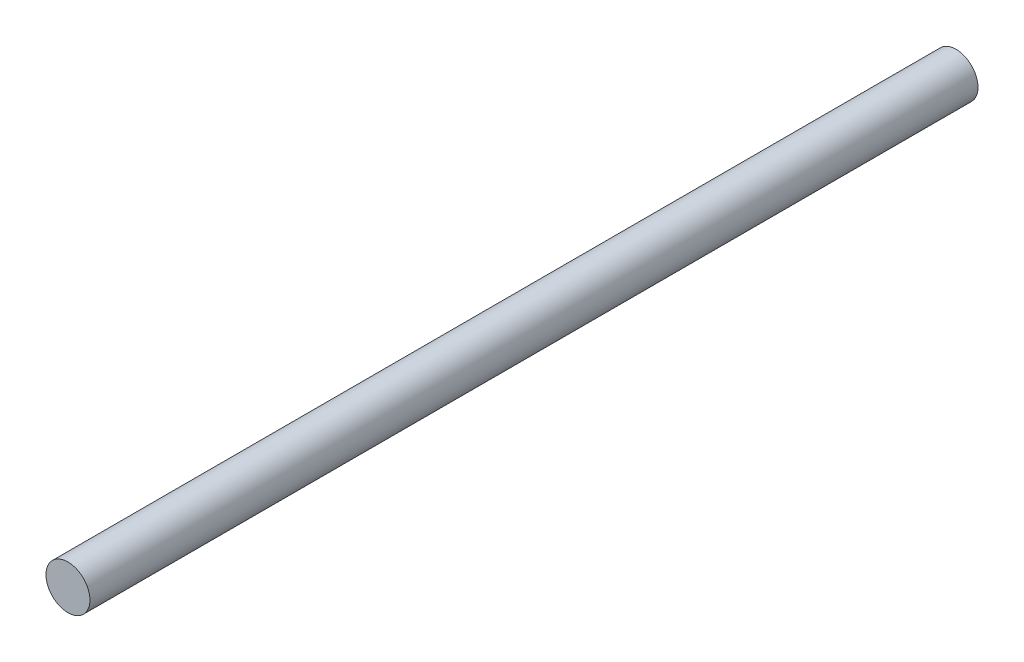
SolidWorks part; units mm, degrees
ref_plane "Front Plane" through (0, 0, 0) normal (0, 0, 1) x (1, 0, 0)
ref_plane "Top Plane" through (0, 0, 0) normal (0, 1, 0) x (1, 0, 0)
ref_plane "Right Plane" through (0, 0, 0) normal (1, 0, 0) x (0, 0, -1)
sketch "Sketch1" plane through (0, 0, 0) normal (0, 0, 1) x (1, 0, 0)
  circle A0 centre (0, 0) radius 25
extrude "Boss-Extrude1" add sketch "Sketch1" along normal blind 1010
sketch "Sketch2" plane through (0, 0, 1010) normal (0, 0, 1) x (1, 0, 0)
  line L0 (0, 37.7299) -> (0, -61.172) construction
  line L1 (-69.9842, 0) -> (115.3286, 0) construction
